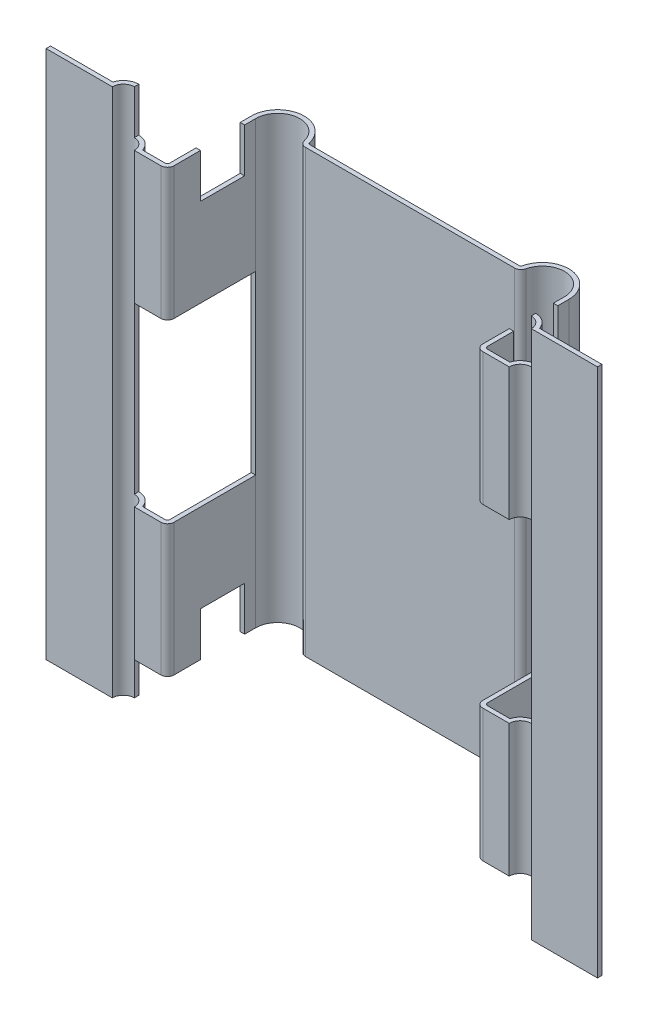
SolidWorks part; units mm, degrees
ref_plane "Front Plane" through (0, 0, 0) normal (0, 0, 1) x (1, 0, 0)
ref_plane "Top Plane" through (0, 0, 0) normal (0, 1, 0) x (1, 0, 0)
ref_plane "Right Plane" through (0, 0, 0) normal (1, 0, 0) x (0, 0, -1)
ref_plane "Plane1" through (0, 0, 0) normal (0, 1, 0) x (1, 0, 0)
sketch "Sketch1" plane through (0, 0, 0) normal (0, 1, 0) x (1, 0, 0)
  line L0 (4.75, 0) -> (6.25, 0)
  line L1 (4.25, 0) -> (3.65, 0)
  line L2 (3.5, 0.15) -> (3.5, 2.0012)
  line L3 (-4.75, 0) -> (-6.25, 0)
  line L4 (-4.25, 0) -> (-3.65, 0)
  line L5 (-3.5, 0.15) -> (-3.5, 2.0012)
  line L6 (2.3675, 2.0012) -> (-2.3675, 2.0012)
  arc A0 (-2.5135, 2.1166) -> (-3.5, 2.0012) centre (-3, 2.0012) ccw
  arc A1 (3.5, 2.0012) -> (2.5135, 2.1166) centre (3, 2.0012) ccw
  arc A2 (-4.25, 0) -> (-4.75, 0) centre (-4.5, 0) ccw
  arc A3 (4.75, 0) -> (4.25, 0) centre (4.5, 0) ccw
  arc A4 (-3.65, 0) -> (-3.5, 0.15) centre (-3.65, 0.15) ccw
  arc A5 (3.5, 0.15) -> (3.65, 0) centre (3.65, 0.15) ccw
  arc A6 (2.3675, 2.0012) -> (2.5135, 2.1166) centre (2.3675, 2.1512) ccw
  arc A7 (-2.5135, 2.1166) -> (-2.3675, 2.0012) centre (-2.3675, 2.1512) ccw
  dimension "D1" = 7
extrude "Extrude-Thin1" add sketch "Sketch1" along normal blind 6 and the other way blind 6 thin thin type one direction wall 0.1
ref_plane "Plane2" through (0, 0, 0) normal (1, 0, 0) x (0, 0, -1)
sketch "Sketch2" plane through (0, 0, 0) normal (1, 0, 0) x (0, 0, -1)
  line L0 (0, 2) -> (2, 2)
  line L1 (2, 2) -> (2, -2)
  line L2 (2, -2) -> (0, -2)
  line L3 (0, -2) -> (0, 2)
  line L4 (0, -6) -> (3, -6)
  line L5 (3, -6) -> (3, -5)
  line L6 (3, -5) -> (0, -5)
  line L7 (0, -5) -> (0, -6)
  line L8 (0, 6) -> (3, 6)
  line L9 (3, 6) -> (3, 5)
  line L10 (3, 5) -> (0, 5)
  line L11 (0, 5) -> (0, 6)
extrude "Extrude1" cut sketch "Sketch2" along normal blind 4.5 and the other way blind 4.5
ref_plane "Plane3" through (0, 0, 0) normal (1, 0, 0) x (0, 0, -1)
sketch "Sketch3" plane through (0, 0, 0) normal (1, 0, 0) x (0, 0, -1)
  line L0 (0.75, 5) -> (1.75, 5)
  line L1 (1.75, 5) -> (1.75, 4)
  line L2 (1.75, 4) -> (0.75, 4)
  line L3 (0.75, 4) -> (0.75, 5)
  line L4 (0.75, -5) -> (1.75, -5)
  line L5 (1.75, -5) -> (1.75, -4)
  line L6 (1.75, -4) -> (0.75, -4)
  line L7 (0.75, -4) -> (0.75, -5)
extrude "Extrude2" cut sketch "Sketch3" along normal blind 10 and the other way blind 10
